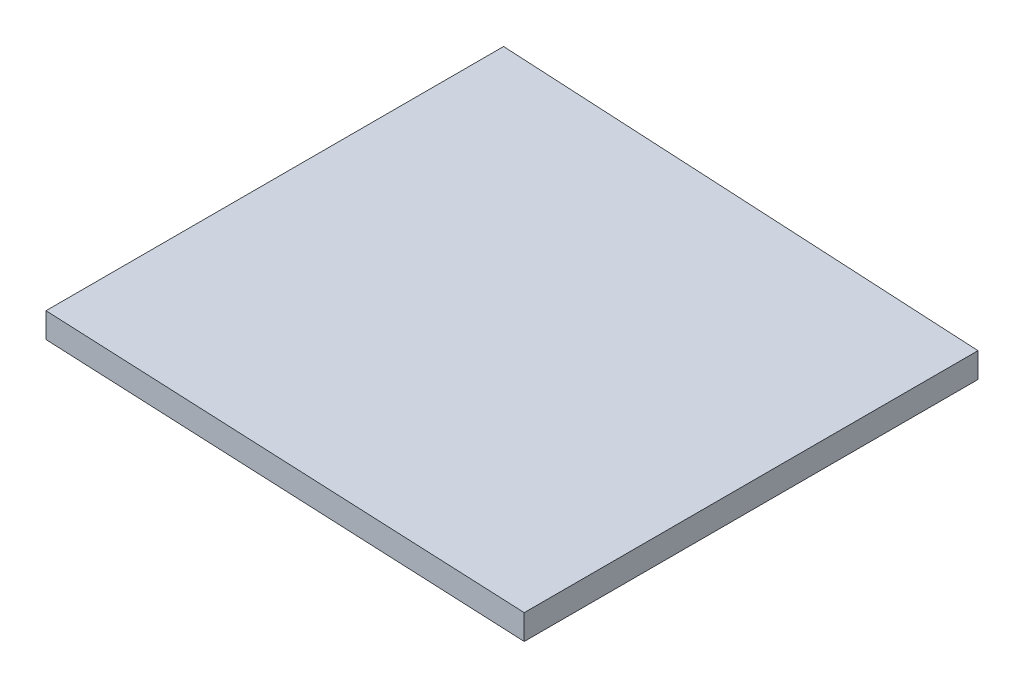
SolidWorks part; units mm, degrees
ref_plane "Plan de face" through (0, 0, 0) normal (0, 0, 1) x (1, 0, 0)
ref_plane "Plan de dessus" through (0, 0, 0) normal (0, 1, 0) x (1, 0, 0)
ref_plane "Plan de droite" through (0, 0, 0) normal (1, 0, 0) x (0, 0, -1)
sketch "Esquisse1" plane through (0, 0, 0) normal (0, 1, 0) x (1, 0, 0)
  line L0 (40.0549, -1.7912) -> (40.0549, 34.5164)
  line L1 (40.0549, 34.5164) -> (0, 36.6127)
  line L2 (0, 36.6127) -> (0, 0)
  line L3 (0, 0) -> (40.0549, -1.7912)
  point P4 (0, 0)
extrude "Boss.-Extru.1" add sketch "Esquisse1" along normal blind 2
